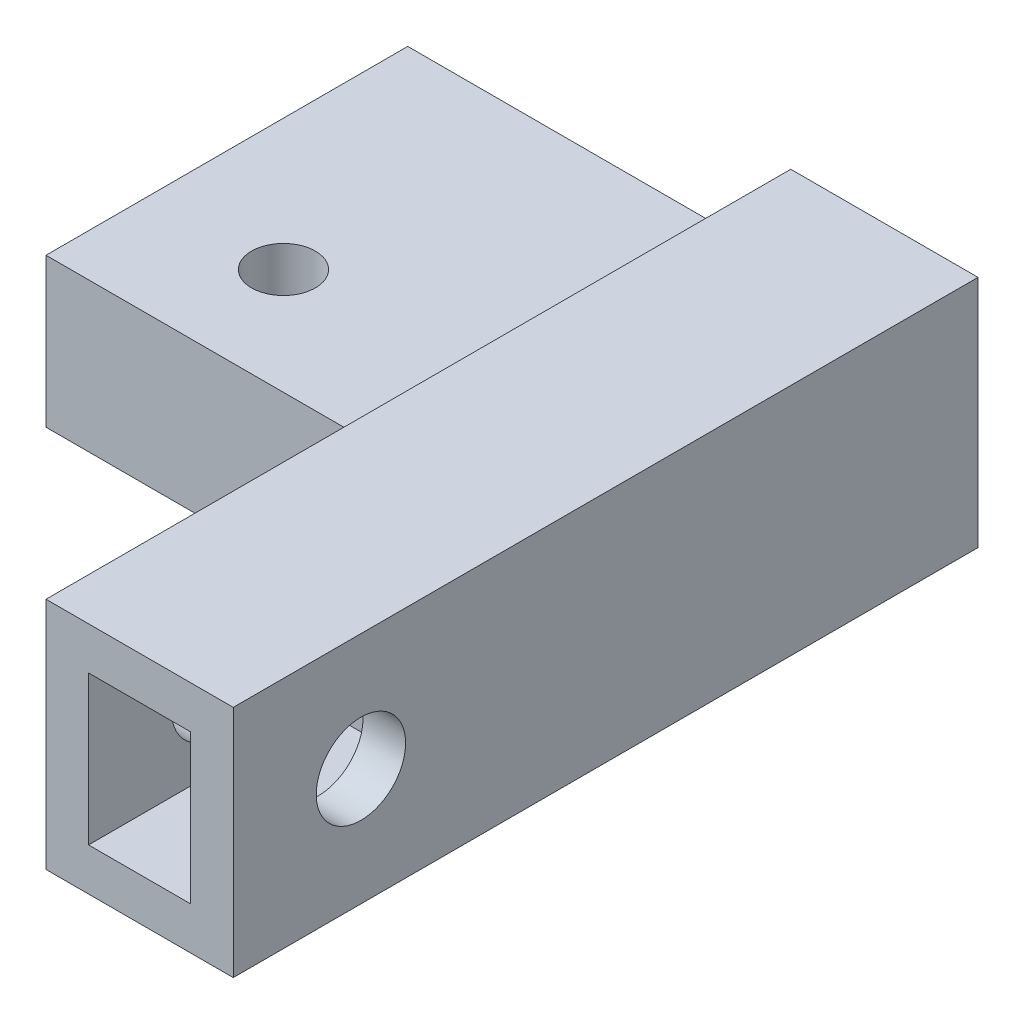
SolidWorks part; units mm, degrees
ref_plane "前视基准面" through (0, 0, 0) normal (0, 0, 1) x (1, 0, 0)
ref_plane "上视基准面" through (0, 0, 0) normal (0, 1, 0) x (1, 0, 0)
ref_plane "右视基准面" through (0, 0, 0) normal (1, 0, 0) x (0, 0, -1)
sketch "草图1" plane through (0, 0, 0) normal (0, 0, 1) x (1, 0, 0)
  line L1 (-4.4, 5.5) -> (4.4, 5.5)
  line L2 (-4.4, 5.5) -> (-4.4, -5.5)
  line L3 (-4.4, -5.5) -> (4.4, -5.5)
  line L4 (4.4, 5.5) -> (4.4, -5.5)
  line L5 (-4.4, 5.5) -> (4.4, -5.5) construction
  line L6 (-4.4, -5.5) -> (4.4, 5.5) construction
  point P0 (0, 0)
extrude "凸台-拉伸1" add sketch "草图1" against normal blind 35
sketch "草图2" plane through (0, 0, 0) normal (0, 0, 1) x (1, 0, 0)
  line L1 (-2.4, 3.5) -> (2.4, 3.5)
  line L2 (-2.4, 3.5) -> (-2.4, -3.5)
  line L3 (-2.4, -3.5) -> (2.4, -3.5)
  line L4 (2.4, 3.5) -> (2.4, -3.5)
  line L5 (-2.4, 3.5) -> (2.4, -3.5) construction
  line L6 (-2.4, -3.5) -> (2.4, 3.5) construction
  point P0 (0, 0)
extrude "切除-拉伸1" cut sketch "草图2" against normal blind 11
sketch "草图3" plane through (-4.4, 0, 0) normal (-1, 0, 0) x (0, 0, 1)
  line L0 (0, 5.5) -> (0, -5.5) construction
  circle A0 centre (-6, 0) radius 2.1
  dimension "D1" = 6
extrude "切除-拉伸2" cut sketch "草图3" against normal blind 11
sketch "草图4" plane through (-4.4, 0, 0) normal (-1, 0, 0) x (0, 0, 1)
  line L1 (-35, -5.5) -> (-18, -5.5)
  line L2 (-35, -5.5) -> (-35, 1.5)
  line L3 (-35, 1.5) -> (-18, 1.5)
  line L4 (-18, -5.5) -> (-18, 1.5)
extrude "凸台-拉伸2" add sketch "草图4" along normal blind 18
sketch "草图5" plane through (0, 1.5, 0) normal (0, 1, 0) x (1, 0, 0)
  line L1 (-22.4, 18) -> (-4.4, 18) construction
  line L3 (-4.4, 18) -> (-4.4, 35) construction
  circle A0 centre (-16.24, 23) radius 1.5
  point P6 (-4.4, 26.5)
  dimension "D1" = 11.84
  dimension "D2" = 5
extrude "切除-拉伸3" cut sketch "草图5" against normal blind 4.5
